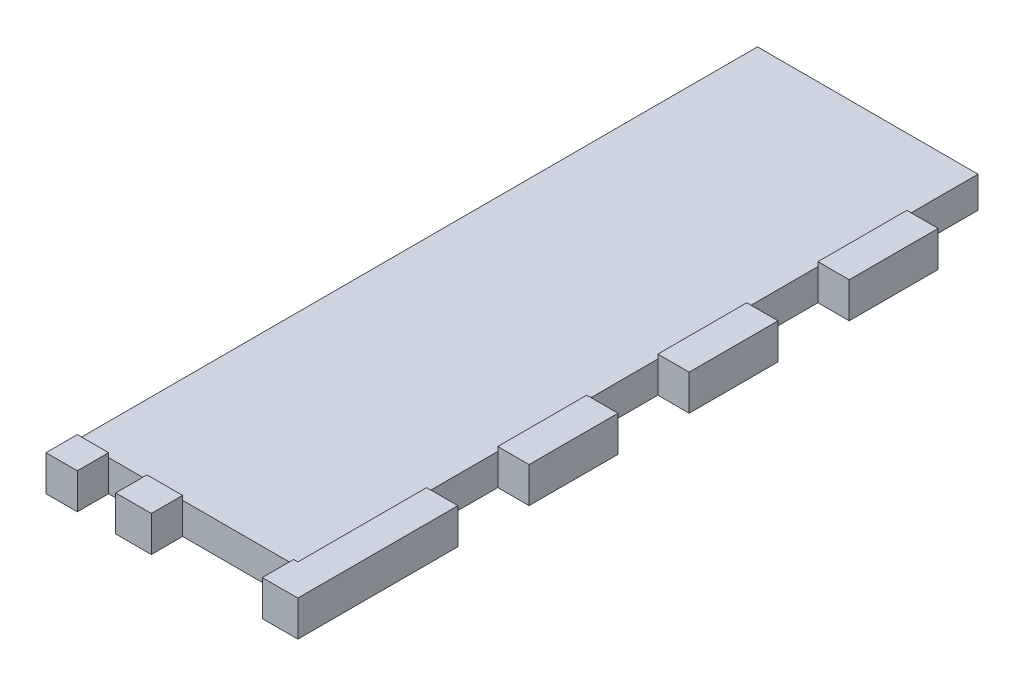
SolidWorks part; units mm, degrees
material "Acrylic (Medium-high impact)"
ref_plane "Front" through (0, 0, 0) normal (0, 0, 1) x (1, 0, 0)
ref_plane "Top" through (0, 0, 0) normal (0, 1, 0) x (1, 0, 0)
ref_plane "Right" through (0, 0, 0) normal (1, 0, 0) x (0, 0, -1)
sketch "Sketch1" plane through (0, 0, 0) normal (0, 0, 1) x (1, 0, 0)
  line L0 (0, 143.002) -> (0, -143.002) construction
  line L1 (-3.302, 133.858) -> (-3.302, -143.002)
  line L2 (-3.302, -143.002) -> (3.302, -143.002)
  line L3 (3.302, 143.002) -> (3.302, -143.002)
  line L4 (3.302, 143.002) -> (-16.256, 143.002)
  line L5 (-5.842, 136.398) -> (-16.256, 136.398)
  line L6 (-16.256, 143.002) -> (-16.256, 136.398)
  line L8 (-28.956, 155.448) -> (16.002, 155.448)
  line L9 (-28.956, 155.448) -> (-28.956, -149.352)
  line L10 (-28.956, -149.352) -> (16.002, -149.352)
  line L11 (16.002, 155.448) -> (16.002, -149.352)
  arc A0 (-3.302, 133.858) -> (-5.842, 136.398) centre (-5.842, 133.858) ccw
  point P2 (0, -143.002)
  point P11 (0, 0)
  dimension "D5" = 2.54
  dimension "D1" = 6.604
  dimension "D2" = 12.954
  dimension "D3" = 6.604
  dimension "D4" = 286.004
  dimension "D6" = 304.8
  dimension "D7" = 6.35
  dimension "D8" = 12.7
  dimension "D9" = 12.7
extrude "Boss-Extrude1" add sketch "Sketch1" along normal blind 5.588
sketch "Sketch2" plane through (16.002, 0, 0) normal (1, 0, 0) x (0, 0, -1)
  line L0 (-5.588, -149.352) -> (-5.588, 155.448) construction
  line L1 (-5.588, -47.752) -> (127, -47.752)
  line L2 (-5.588, -47.752) -> (-5.588, -149.352)
  line L3 (-5.588, -149.352) -> (127, -149.352)
  line L4 (127, -47.752) -> (127, -149.352)
  line L5 (14.4, -101.092) -> (14.4, -96.012)
  line L6 (36.4, -96.012) -> (36.4, -101.092)
  line L7 (8.4, -116.592) -> (8.4, -111.512)
  line L8 (11.4, -116.592) -> (11.4, -111.512)
  line L9 (8.4, -85.592) -> (8.4, -80.512)
  line L10 (11.4, -85.592) -> (11.4, -80.512)
  line L11 (25.4, -96.012) -> (25.4, -101.092) construction
  line L12 (42.4, -116.592) -> (42.4, -111.512)
  line L13 (39.4, -116.592) -> (39.4, -111.512)
  line L14 (39.4, -85.592) -> (39.4, -80.512)
  line L15 (42.4, -85.592) -> (42.4, -80.512)
  line L16 (0, -149.352) -> (0, 155.448) construction
  line L17 (124.206, -60.452) -> (124.206, -77.3853) construction
  line L18 (127, -47.752) -> (121.412, -47.752)
  line L19 (127, -47.752) -> (127, -60.452)
  line L20 (127, -60.452) -> (121.412, -60.452)
  line L21 (121.412, -47.752) -> (121.412, -60.452)
  line L22 (127, -107.0187) -> (121.412, -107.0187)
  line L23 (127, -107.0187) -> (127, -119.7187)
  line L24 (127, -119.7187) -> (121.412, -119.7187)
  line L25 (121.412, -107.0187) -> (121.412, -119.7187)
  line L26 (127, -136.652) -> (121.412, -136.652)
  line L27 (127, -136.652) -> (127, -149.352)
  line L28 (127, -149.352) -> (121.412, -149.352)
  line L29 (121.412, -136.652) -> (121.412, -149.352)
  line L30 (127, -77.3853) -> (121.412, -77.3853)
  line L31 (127, -77.3853) -> (127, -90.0853)
  line L32 (127, -90.0853) -> (121.412, -90.0853)
  line L33 (121.412, -77.3853) -> (121.412, -90.0853)
  line L34 (124.206, -90.0853) -> (124.206, -107.0187) construction
  line L35 (124.206, -119.7187) -> (124.206, -136.652) construction
  arc A0 (14.4, -101.092) -> (36.4, -101.092) centre (25.4, -101.092) ccw
  arc A1 (36.4, -96.012) -> (14.4, -96.012) centre (25.4, -96.012) ccw
  arc A2 (8.4, -116.592) -> (11.4, -116.592) centre (9.9, -116.592) ccw
  arc A3 (11.4, -111.512) -> (8.4, -111.512) centre (9.9, -111.512) ccw
  arc A4 (8.4, -85.592) -> (11.4, -85.592) centre (9.9, -85.592) ccw
  arc A5 (11.4, -80.512) -> (8.4, -80.512) centre (9.9, -80.512) ccw
  arc A6 (42.4, -116.592) -> (39.4, -116.592) centre (40.9, -116.592) cw
  arc A7 (39.4, -111.512) -> (42.4, -111.512) centre (40.9, -111.512) cw
  arc A8 (42.4, -85.592) -> (39.4, -85.592) centre (40.9, -85.592) cw
  arc A9 (39.4, -80.512) -> (42.4, -80.512) centre (40.9, -80.512) cw
  point P44 (25.4, -98.552)
  point P47 (-5.588, -98.552)
  line M17 (0, -149.352) -> (0, 155.448)
  line M19 (-5.588, 155.448) -> (-5.588, -149.352)
  line M20 (-5.588, -149.352) -> (0, -149.352)
  dimension "D1" = 22
  dimension "D6" = 1.5
  dimension "D10" = 1.5
  dimension "D2" = 5.08
  dimension "D3" = 5.08
  dimension "D4" = 15.5
  dimension "D5" = 15.5
  dimension "D7" = 15.5
  dimension "D8" = 15.5
  dimension "D9" = 5.08
  dimension "D11" = 25.4
  dimension "D12" = 50.8
  dimension "D13" = 101.6
  dimension "D14" = 12.7
  dimension "D15" = 5.588
extrude "Boss-Extrude2" add sketch "Sketch2" against normal blind 5.588 contours L33 L30 L4 L20 L21 L1 L3 L29 L26 L24 L25 L22 L32 A5 L10 A4 L9 A3 L8 A2 L7 A1 L6 A0 L5 L13 A7 L12 A6 L14 A9 L15 A8 M17 | L1 M19 M20 M17
sketch "Sketch3" plane through (10.414, 0, 0) normal (-1, 0, 0) x (0, 0, 1)
  line L0 (-121.412, -136.652) -> (-121.412, -149.352) construction
  line L1 (-121.412, -143.764) -> (0, -143.764)
  line L2 (-121.412, -143.764) -> (-121.412, -149.352)
  line L3 (-121.412, -149.352) -> (0, -149.352)
  line L4 (0, -143.764) -> (0, -149.352)
  dimension "D1" = 5.588
extrude "Boss-Extrude3" add sketch "Sketch3" along normal up to surface (39.37 mm away) up to face at (-28.956, 3.048, 2.794)
sketch "Sketch4" plane through (0, -149.352, 0) normal (0, -1, 0) x (1, 0, 0)
  line L0 (10.414, -22.987) -> (10.414, -35.687)
  line L1 (16.002, 5.588) -> (10.414, 5.588)
  line L2 (16.002, 5.588) -> (16.002, -7.112)
  line L3 (16.002, -7.112) -> (10.414, -7.112)
  line L4 (10.414, 5.588) -> (10.414, -7.112)
  line L5 (16.002, -22.987) -> (10.414, -22.987)
  line L6 (16.002, -22.987) -> (16.002, -35.687)
  line L7 (16.002, -35.687) -> (10.414, -35.687)
  line L8 (10.414, -51.562) -> (10.414, -64.262)
  line L9 (16.002, -51.562) -> (10.414, -51.562)
  line L10 (16.002, -51.562) -> (16.002, -64.262)
  line L11 (16.002, -64.262) -> (10.414, -64.262)
  line L12 (10.414, -80.137) -> (10.414, -92.837)
  line L13 (16.002, -80.137) -> (10.414, -80.137)
  line L14 (16.002, -80.137) -> (16.002, -92.837)
  line L15 (16.002, -92.837) -> (10.414, -92.837)
  line L36 (-6.477, 5.588) -> (-6.477, -121.412) construction
  line L37 (-28.956, 5.588) -> (16.002, 5.588) construction
  line L38 (-28.956, -121.412) -> (16.002, -121.412) construction
  line L39 (-23.368, 5.588) -> (-23.368, -121.412)
  line L40 (16.002, 5.588) -> (10.414, 5.588)
  line L41 (16.002, 5.588) -> (16.002, -121.412)
  line L42 (16.002, -121.412) -> (10.414, -121.412)
  line L43 (10.414, 5.588) -> (10.414, -121.412)
  line L44 (-28.956, -121.412) -> (-23.368, -121.412)
  line L45 (-28.956, 5.588) -> (-28.956, -121.412)
  line L46 (-28.956, 5.588) -> (-23.368, 5.588)
  line L47 (-28.956, -121.412) -> (-23.368, -121.412)
  line L48 (-28.956, -107.95) -> (-28.956, -121.412)
  line L49 (-28.956, -107.95) -> (-23.368, -107.95)
  line L50 (-23.368, -107.95) -> (-23.368, -121.412)
  line L51 (-28.956, -106.3625) -> (-22.606, -106.3625)
  line L52 (-28.956, -93.6625) -> (-28.956, -106.3625)
  line L53 (-28.956, -93.6625) -> (-22.606, -93.6625)
  line L54 (-22.606, -93.6625) -> (-22.606, -106.3625)
  line L55 (-28.956, -92.075) -> (-22.606, -92.075)
  line L56 (-28.956, -79.375) -> (-28.956, -92.075)
  line L57 (-28.956, -79.375) -> (-22.606, -79.375)
  line L58 (-22.606, -79.375) -> (-22.606, -92.075)
  line L59 (-28.956, -77.7875) -> (-22.606, -77.7875)
  line L60 (-28.956, -65.0875) -> (-28.956, -77.7875)
  line L61 (-28.956, -65.0875) -> (-22.606, -65.0875)
  line L62 (-22.606, -65.0875) -> (-22.606, -77.7875)
  line L63 (-28.956, -63.5) -> (-22.606, -63.5)
  line L64 (-28.956, -50.8) -> (-28.956, -63.5)
  line L65 (-28.956, -50.8) -> (-22.606, -50.8)
  line L66 (-22.606, -50.8) -> (-22.606, -63.5)
  line L67 (-28.956, -92.837) -> (-23.368, -92.837)
  line L68 (-28.956, -80.137) -> (-28.956, -92.837)
  line L69 (-28.956, -80.137) -> (-23.368, -80.137)
  line L70 (-23.368, -80.137) -> (-23.368, -92.837)
  line L71 (-28.956, -64.262) -> (-23.368, -64.262)
  line L72 (-28.956, -51.562) -> (-28.956, -64.262)
  line L73 (-28.956, -51.562) -> (-23.368, -51.562)
  line L74 (-23.368, -51.562) -> (-23.368, -64.262)
  line L75 (-28.956, -35.687) -> (-23.368, -35.687)
  line L76 (-28.956, -22.987) -> (-28.956, -35.687)
  line L77 (-28.956, -22.987) -> (-23.368, -22.987)
  line L78 (-23.368, 5.588) -> (-23.368, -7.112)
  line L79 (-28.956, -7.112) -> (-23.368, -7.112)
  line L80 (-28.956, 5.588) -> (-28.956, -7.112)
  line L81 (-28.956, 5.588) -> (-23.368, 5.588)
  line L82 (-23.368, -22.987) -> (-23.368, -35.687)
  line L83 (-16.51, 2.794) -> (-23.368, 2.794) construction
  line L85 (-28.956, 5.588) -> (-22.606, 5.588)
  line L86 (-28.956, 5.588) -> (-28.956, 0)
  line L87 (-28.956, 0) -> (-22.606, 0)
  line L88 (-22.606, 5.588) -> (-22.606, 0)
  line L92 (9.652, 5.588) -> (9.652, 0)
  line L93 (9.652, 5.588) -> (16.002, 5.588)
  line L94 (16.002, 5.588) -> (16.002, 0)
  line L95 (9.652, 0) -> (16.002, 0)
  line L100 (-9.652, 5.588) -> (-9.652, 0) [skipped]
  line L101 (-9.652, 0) -> (-3.302, 0) [skipped]
  line L102 (-3.302, 5.588) -> (-3.302, 0) [skipped]
  line L103 (-9.652, 5.588) -> (-3.302, 5.588) [skipped]
  line L104 (-10.16, 0) -> (-16.51, 0)
  line L105 (-10.16, 0) -> (-10.16, 5.588)
  line L106 (-10.16, 5.588) -> (-16.51, 5.588)
  line L107 (-16.51, 0) -> (-16.51, 5.588)
  line L108 (-10.16, 2.794) -> (-3.302, 2.794) construction
  line L109 (-3.302, 5.588) -> (-3.302, 0) construction
  line L110 (-23.368, 5.588) -> (-16.51, 5.588)
  line L115 (-28.956, 5.588) -> (16.002, 5.588)
  line L116 (-28.956, 5.588) -> (-28.956, 0)
  line L117 (-28.956, 0) -> (16.002, 0)
  line L118 (16.002, 5.588) -> (16.002, 0)
  line L119 (-28.956, 5.588) -> (16.002, 5.588)
  line L120 (-28.956, 5.588) -> (-28.956, 0)
  line L121 (-28.956, 0) -> (16.002, 0)
  line L122 (16.002, 5.588) -> (16.002, 0)
  line L123 (-22.606, 0) -> (-16.51, 0)
  line L124 (-10.16, 5.588) -> (10.414, 5.588)
  line L125 (-10.16, 0) -> (9.652, 0)
  line L126 (10.414, -108.712) -> (10.414, -121.412)
  line L127 (16.002, -108.712) -> (10.414, -108.712)
  line L128 (16.002, -108.712) -> (16.002, -121.412)
  line L129 (16.002, -121.412) -> (10.414, -121.412)
  line M38 (16.002, -121.412) -> (16.002, 5.588)
  line M41 (-28.956, -121.412) -> (16.002, -121.412)
  dimension "D1" = 5.588
  dimension "D2" = 12.7
  dimension "D4" = 5.588
  dimension "D5" = 6.35
  dimension "D7" = 6.35
  dimension "D3" = 5
  dimension "D6" = 3
sketch "Sketch6" plane through (0, 0, 5.588) normal (0, 0, 1) x (1, 0, 0)
  line L1 (16.002, -60.452) -> (10.414, -60.452)
  line L2 (16.002, -60.452) -> (16.002, -77.3853)
  line L3 (16.002, -77.3853) -> (10.414, -77.3853)
  line L4 (10.414, -60.452) -> (10.414, -77.3853)
  line L5 (16.002, -90.0853) -> (10.414, -90.0853)
  line L6 (16.002, -90.0853) -> (16.002, -107.0187)
  line L7 (16.002, -107.0187) -> (10.414, -107.0187)
  line L8 (10.414, -90.0853) -> (10.414, -107.0187)
  line L9 (16.002, -119.7187) -> (10.414, -119.7187)
  line L10 (16.002, -119.7187) -> (16.002, -136.652)
  line L11 (16.002, -136.652) -> (10.414, -136.652)
  line L12 (10.414, -119.7187) -> (10.414, -136.652)
sketch "Sketch7" plane through (16.002, 0, 0) normal (1, 0, 0) x (0, 0, -1)
  line L1 (-5.588, 180.723) -> (327.0227, 180.723)
  line L2 (-5.588, 180.723) -> (-5.588, -143.002)
  line L3 (-5.588, -143.002) -> (327.0227, -143.002)
  line L4 (327.0227, 180.723) -> (327.0227, -143.002)
  line L5 (-5.588, -149.352) -> (-5.588, 155.448) construction
  line L6 (121.412, -143.002) -> (0, -143.002) construction
  point P10 (160.7174, -143.002)
extrude "Cut-Extrude1" cut sketch "Sketch7" against normal through all
extrude "Cut-Extrude2" cut sketch "Sketch4" against normal blind 6.35 contours L7 L5 L0 M38 | L11 L9 L8 M38 | L15 L13 L12 M38 | L127 L43 M38 M41 | L86 L85 L88 L87
sketch "Sketch8" plane through (0, -149.352, 0) normal (0, -1, 0) x (1, 0, 0)
  line L1 (-23.368, 5.588) -> (-16.51, 5.588)
  line L2 (-23.368, 5.588) -> (-23.368, 0)
  line L3 (-23.368, 0) -> (-16.51, 0)
  line L4 (-16.51, 5.588) -> (-16.51, 0)
  line L5 (-10.16, 5.588) -> (9.652, 5.588)
  line L6 (-10.16, 5.588) -> (-10.16, 0)
  line L7 (-10.16, 0) -> (9.652, 0)
  line L8 (9.652, 5.588) -> (9.652, 0)
extrude "Cut-Extrude4" cut sketch "Sketch8" against normal through all
